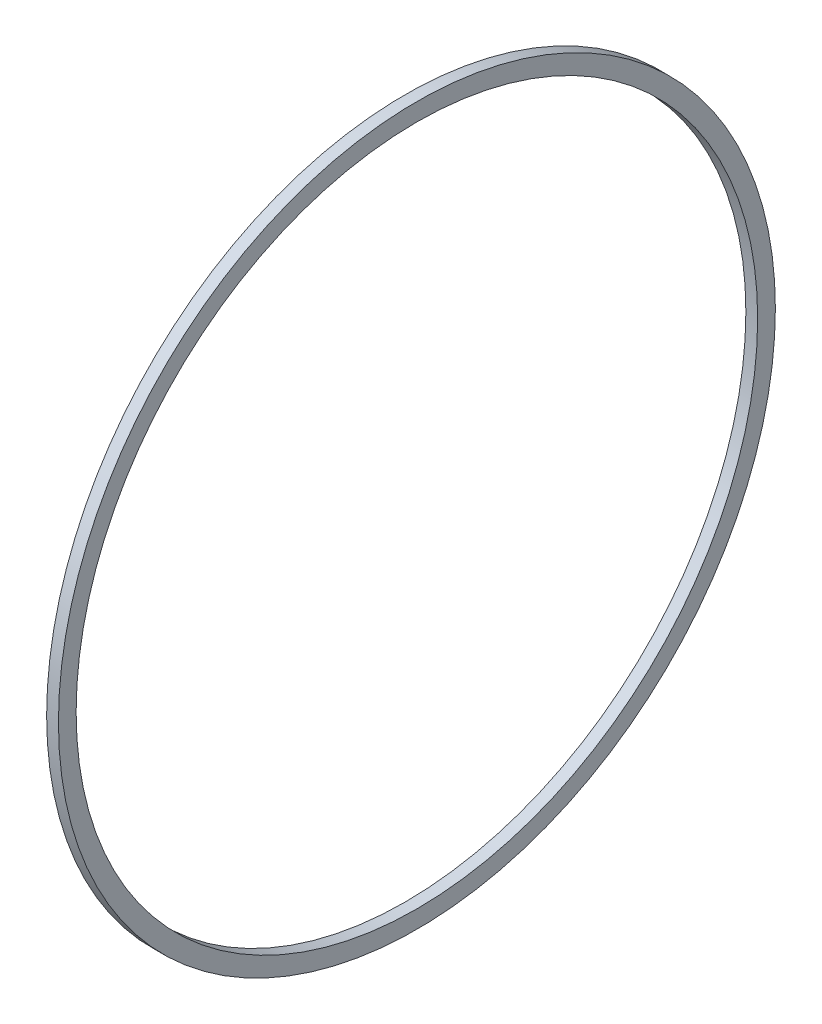
SolidWorks part; units mm, degrees
ref_plane "Front Plane" through (0, 0, 0) normal (0, 0, 1) x (1, 0, 0)
ref_plane "Top Plane" through (0, 0, 0) normal (0, 1, 0) x (1, 0, 0)
ref_plane "Right Plane" through (0, 0, 0) normal (1, 0, 0) x (0, 0, -1)
sketch "Sketch1" plane through (0, 0, 0) normal (1, 0, 0) x (0, 0, -1)
  circle A0 centre (0, 0) radius 60.75
  circle A1 centre (0, 0) radius 57.75
  dimension "D1" = 3
  dimension "D2" = 115.5
extrude "Boss-Extrude1" add sketch "Sketch1" along normal blind 2
